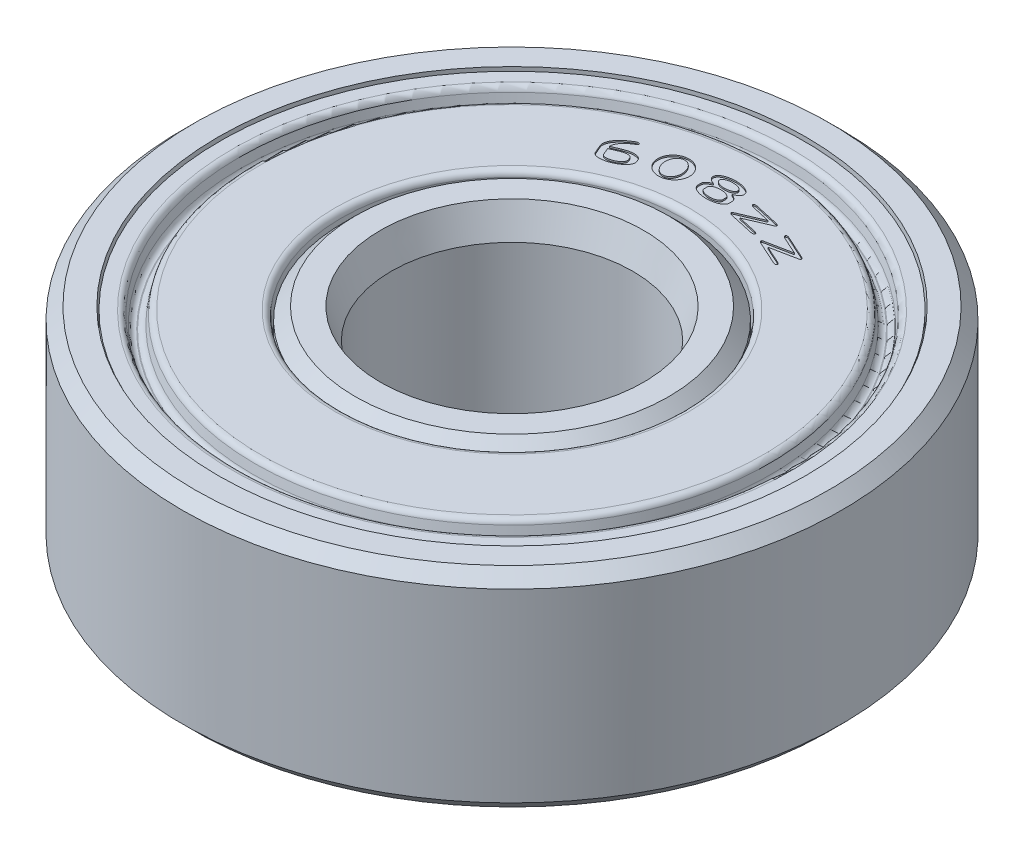
SolidWorks part; units mm, degrees
ref_plane "Front Plane" through (0, 0, 0) normal (0, 0, 1) x (1, 0, 0)
ref_plane "Top Plane" through (0, 0, 0) normal (0, 1, 0) x (1, 0, 0)
ref_plane "Right Plane" through (0, 0, 0) normal (1, 0, 0) x (0, 0, -1)
sketch "Sketch1" plane through (0, 0, 0) normal (0, 0, 1) x (1, 0, 0)
  line L0 (0, -3.9412) -> (0, 3.9412) construction
  line L2 (11, -3.49) -> (9.8, -3.49)
  line L3 (11, -3.49) -> (11, 3.49)
  line L4 (11, 3.49) -> (9.8, 3.49)
  line L5 (9.8, -3.49) -> (9.8, 3.49)
  point P7 (9.8, 0)
  dimension "D1" = 22
  dimension "D2" = 6.98
  dimension "D3" = 1.2
revolve "outer race" add sketch "Sketch1" angle 360 about L0
chamfer "chamf outer race" distance 0.4 angle 45 2 edges at (0, -3.49, -11) (0, 3.49, -11)
sketch "Sketch2" plane through (0, 0, 0) normal (0, 0, 1) x (1, 0, 0)
  line L0 (9.8, 3.49) -> (-9.8, 3.49) construction
  line L1 (4.03, 3.49) -> (5.63, 3.49)
  line L2 (4.03, 3.49) -> (4.03, -3.49)
  line L3 (4.03, -3.49) -> (5.63, -3.49)
  line L4 (5.63, 3.49) -> (5.63, -3.49)
  line L5 (-9.8, -3.49) -> (9.8, -3.49) construction
  line L6 (0, 0) -> (0, 3.49) construction
  dimension "D1" = 8.06
  dimension "D2" = 1.6
revolve "inner race" add sketch "Sketch2" angle 360 about L6
chamfer "chamf small" distance 0.4 angle 45 2 edges at (0, 3.49, -5.63) (0, -3.49, -5.63)
chamfer "chamf axle" distance 1 angle 20 2 edges at (0, -3.49, -4.03) (0, 3.49, -4.03)
sketch "Sketch3" plane through (0, 0, 0) normal (0, 0, 1) x (1, 0, 0)
  line L0 (9.75, 3.39) -> (9.15, 3.39)
  line L1 (9.15, 3.39) -> (9.15, 2.79)
  line L2 (9.15, 2.79) -> (8.55, 2.79)
  line L3 (8.55, 2.79) -> (8.55, 3.39)
  line L4 (8.55, 3.39) -> (5.7, 3.39)
  line L5 (5.7, 3.39) -> (5.7, 2.29)
  line L6 (5.7, 2.29) -> (9.15, 2.29)
  line L7 (9.15, 2.29) -> (9.75, 2.79)
  line L8 (9.75, 2.79) -> (9.75, 3.39)
  line L9 (10.6, 3.49) -> (-10.6, 3.49) construction
  dimension "D1" = 0.1
  dimension "D2" = 0.6
  dimension "D3" = 0.6
  dimension "D4" = 0.6
  dimension "D5" = 5.7
  dimension "D6" = 9.75
  dimension "D7" = 1.1
  dimension "D8" = 0.6
ref_axis "Axis1" through (0, 3.839, 0) along (0, -1, 0)
revolve "cover" add sketch "Sketch3" angle 360 about axis through (0, 3.839, 0) along (0, -1, 0)
draft "draft pinch" type of draft neutral plane draft angle 12 faces to draft 2 face at (0, 3.39, 8.55) face at (0, 2.79, 9.15) neutral plane through (9.75, 3.39, 0) neutral plane normal (0, 1, 0) parameters "D1"=12
fillet "fillet cover" radius 0.2 5 edges at (0, 3.39, 5.7) (0, 3.39, 8.55) (0, 2.79, -8.6775) (0, 2.79, -9.0225) (0, 3.39, 9.15)
sketch "Sketch6" plane through (0, 0, 0) normal (0, 0, 1) x (1, 0, 0)
  line L0 (8.8605, 2.79) -> (-8.8605, 2.79) construction
  line L1 (8.8605, 2.79) -> (9.7605, 2.79)
  line L2 (8.8605, 2.79) -> (8.8605, 3.39)
  line L3 (8.8605, 3.39) -> (9.7605, 3.39)
  line L4 (9.7605, 2.79) -> (9.7605, 3.39)
  line L5 (9.75, 2.79) -> (-9.75, 2.79) construction
  line L6 (9.75, 3.39) -> (-9.75, 3.39) construction
  dimension "D1" = 0.9
extrude "Cut-Extrude2" [suppressed] cut sketch "Sketch6" against normal blind 0.5
pattern_circular "CirPattern1" [suppressed] count 8 over 360 about axis through (0, 3.839, 0) along (0, -1, 0)
mirror "Mirror5" about plane through (0, 0, 0) normal (0, 1, 0) of bodies 103 106
sketch "Sketch4" plane through (0, 3.39, 0) normal (0, 1, 0) x (1, 0, 0)
  line L0 (0, 0) -> (-3.25, 5.6292) construction
  line L1 (0, 0) -> (3.25, 5.6292) construction
  line L2 (3.25, 5.6292) -> (-3.25, 5.6292) construction
  arc A0 (-3.25, 5.6292) -> (3.25, 5.6292) centre (0, 0) cw construction
  text T0 "608zz" font "DS ISO 1" height 1
  point P3 (0, 5.6292)
  dimension "D1" = 60
  dimension "D2" = 6.5
extrude "cut label" cut sketch "Sketch4" against normal blind 0.05
